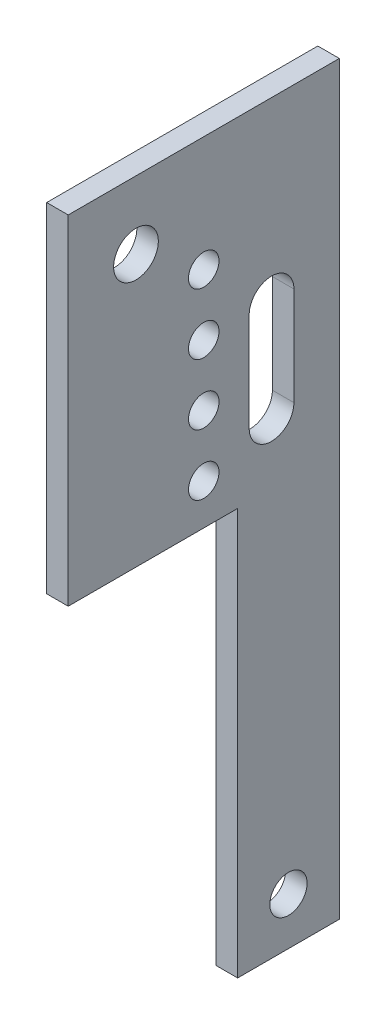
SolidWorks part; units mm, degrees
ref_plane "Front Plane" through (0, 0, 0) normal (0, 0, 1) x (1, 0, 0)
ref_plane "Top Plane" through (0, 0, 0) normal (0, 1, 0) x (1, 0, 0)
ref_plane "Right Plane" through (0, 0, 0) normal (1, 0, 0) x (0, 0, -1)
sketch "Sketch1" plane through (0, 0, 0) normal (1, 0, 0) x (0, 0, -1)
  line L0 (40, 0) -> (0, 0)
  line L2 (0, 0) -> (0, -50)
  line L4 (40, 0) -> (40, -50)
  line L8 (40, -50) -> (40, -110)
  line L9 (40, -110) -> (25, -110)
  line L10 (25, -110) -> (25, -50)
  line L11 (25, -50) -> (0, -50)
  line L12 (30, -26.1084) -> (30, -40.6292) construction
  line L13 (33.3, -26.1084) -> (33.3, -40.6292)
  line L14 (26.7, -26.1084) -> (26.7, -40.6292)
  circle A1 centre (10, -10) radius 3.3
  circle A2 centre (20, -16.9748) radius 2.25
  circle A3 centre (20, -25.9748) radius 2.25
  circle A4 centre (20, -34.9748) radius 2.25
  circle A5 centre (20, -43.9748) radius 2.25
  circle A7 centre (32.5, -103) radius 2.75
  arc A8 (33.3, -26.1084) -> (26.7, -26.1084) centre (30, -26.1084) ccw
  arc A9 (26.7, -40.6292) -> (33.3, -40.6292) centre (30, -40.6292) ccw
  point P17 (30, -33.3688)
  point P26 (32.5, -110)
  dimension "D3" = 6.6
  dimension "D9" = 4.5
  dimension "D10" = 4.5
  dimension "D11" = 4.5
  dimension "D14" = 4.5
  dimension "D7" = 7
  dimension "D17" = 5.5
  dimension "D18" = 3.3
  dimension "D1" = 50
  dimension "D2" = 40
  dimension "D5" = 10
  dimension "D6" = 60
  dimension "D8" = 10
  dimension "D12" = 9
  dimension "D13" = 9
  dimension "D15" = 9
  dimension "D16" = 20
  dimension "D20" = 15
  dimension "D21" = 50
extrude "Boss-Extrude1" add sketch "Sketch1" along normal blind 3.175
